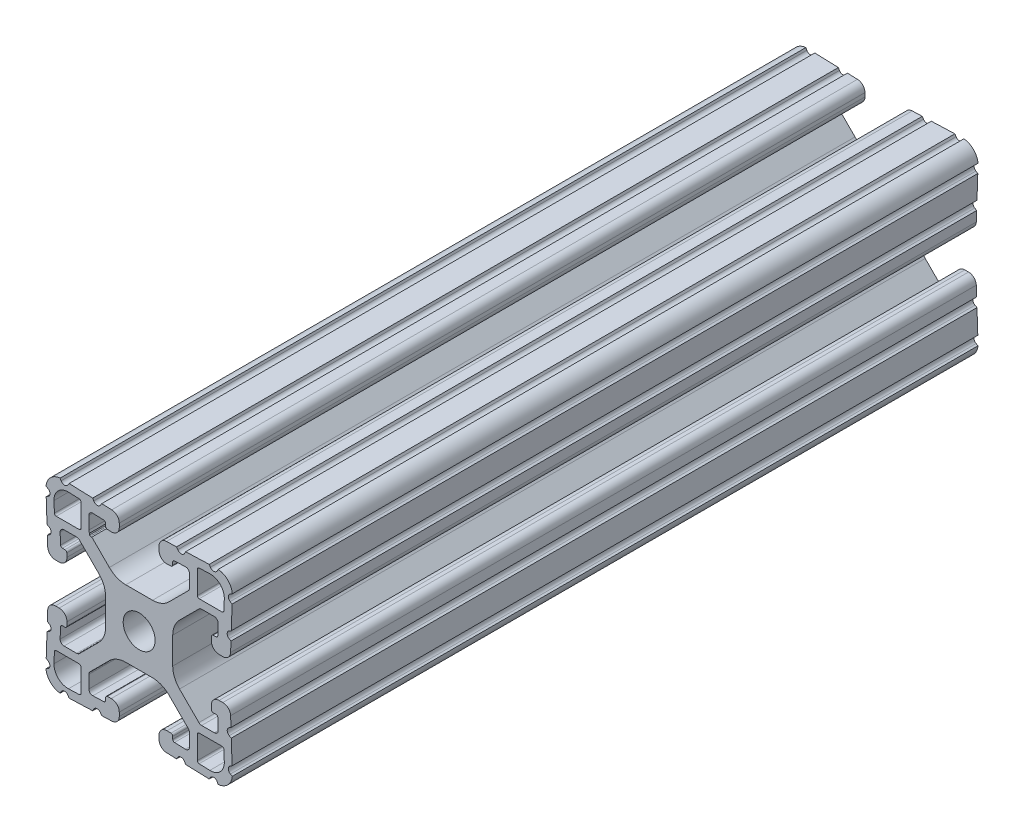
SolidWorks part; units mm, degrees
ref_plane "Front Plane" through (0, 0, 0) normal (0, 0, 1) x (1, 0, 0)
ref_plane "Top Plane" through (0, 0, 0) normal (0, 1, 0) x (1, 0, 0)
ref_plane "Right Plane" through (0, 0, 0) normal (1, 0, 0) x (0, 0, -1)
sketch "Sketch2" plane through (0, 0, 0) normal (0, 0, 1) x (1, 0, 0)
  line L0 (0, 19.05) -> (0, -19.05) construction
  line L1 (-19.05, 0) -> (19.05, 0) construction
  line L2 (4.064, -19.05) -> (19.05, -19.05) construction
  line L3 (19.05, -19.05) -> (19.05, -4.064) construction
  line L4 (4.064, -19.05) -> (4.064, -15.8768) construction
  line L5 (4.064, -15.8768) -> (13.7215, -15.8768) construction
  line L6 (13.7215, -15.8768) -> (4.7027, -6.858) construction
  line L7 (0, 0) -> (19.05, -19.05) construction
  line L8 (19.05, -4.064) -> (15.8768, -4.064) construction
  line L9 (15.8768, -4.064) -> (15.8768, -13.7215) construction
  line L10 (15.8768, -13.7215) -> (6.858, -4.7027) construction
  line L11 (11.3674, -9.2121) -> (9.2121, -11.3674) construction
  line L12 (10.287, -12.4423) -> (10.287, -15.8768) construction
  line L13 (15.7642, -19.0481) -> (4.064, -18.6395) construction
  line L14 (4.064, -18.6395) -> (4.2014, -14.7049) construction
  line L15 (4.2014, -14.7049) -> (6.858, -14.7977) construction
  line L16 (6.858, -14.7977) -> (6.858, -15.8768) construction
  line L17 (19.05, 4.064) -> (19.05, -4.064) construction
  line L18 (-19.05, -19.05) -> (19.05, -19.05) construction
  line L19 (-19.05, -19.05) -> (-19.05, 19.05) construction
  line L20 (-19.05, 19.05) -> (19.05, 19.05) construction
  line L21 (19.05, -19.05) -> (19.05, 19.05) construction
  line L22 (8.5725, -18.7969) -> (8.6004, -17.9973) construction
  line L23 (15.24, -19.0298) -> (15.2679, -18.2301) construction
  circle A0 centre (0, 0) radius 3.2639 construction
  arc A1 (18.1201, -18.1201) -> (15.7642, -19.0481) centre (15.875, -15.875) cw construction
  point P8 (0, -6.858)
  point P16 (10.2898, -10.2898)
  point P28 (11.8872, -11.8872)
  point P34 (8.5725, -18.7969)
  point P36 (15.24, -19.0298)
  point P38 (19.05, 0)
  dimension "D7" = 1.6002
  dimension "Center Hole Diameter" = 6.5278
  dimension "Corner Radius" = 3.175
  dimension "Rail Height" = 19.05
  dimension "Rail Width" = 19.05
  dimension "T-Slot Width" = 4.064
  dimension "Slot Depth" = 12.192
  dimension "D1" = 3.048
  dimension "D3" = 2
  dimension "Flange Thickness" = 3.937
  dimension "D4" = 3.1732
  dimension "D2" = 20.574
  dimension "D5" = 13.716
  dimension "D6" = 7.1628
  dimension "D8" = 15.24
  dimension "D9" = 8.5725
  dimension "D10" = 0.8001
sketch "Sketch3" plane through (0, 0, 0) normal (1, 0, 0) x (0, 0, -1)
  line L0 (-76.2, 19.05) -> (76.2, 19.05) construction
  line L1 (-25.4, 0) -> (25.4, 0) construction
  dimension "Length" = 152.4
  dimension "D1" = 50.8
sketch "Sketch4" plane through (0, 0, 0) normal (0, 0, 1) x (1, 0, 0)
  line L1 (6.858, -14.7977) -> (6.858, -15.8768) construction
  line L2 (11.8872, -12.2682) -> (11.8872, -16.9436)
  line L3 (12.2549, -17.3243) -> (14.4454, -17.4008)
  line L7 (12.2682, -11.8872) -> (16.9436, -11.8872)
  line L9 (17.3243, -12.2549) -> (17.4008, -14.4454)
  line L22 (0, 0) -> (19.05, -19.05) construction
  line L23 (15.7642, -19.0481) -> (5.5961, -18.693)
  line L24 (4.064, -17.1065) -> (4.064, -16.344)
  line L25 (5.7069, -14.7575) -> (6.4903, -14.7848)
  line L26 (6.858, -15.1656) -> (6.858, -15.6891)
  line L27 (7.2257, -16.0699) -> (9.4655, -16.1481)
  line L28 (10.287, -15.3549) -> (10.287, -12.771)
  line L29 (10.0545, -12.2098) -> (6.0939, -8.2492)
  line L30 (2.7353, -6.858) -> (0, -6.858)
  line L31 (13.7215, -15.8768) -> (4.7027, -6.858) construction
  line L32 (4.064, -19.05) -> (19.05, -19.05) construction
  line L33 (4.064, -19.05) -> (4.064, -15.8768) construction
  line L34 (0, 19.05) -> (0, -19.05) construction
  line L35 (0, -3.2639) -> (0, -6.858)
  line L36 (0, 0) -> (19.05, -19.05) construction
  line L46 (10.287, -12.4423) -> (10.287, -15.8768) construction
  line L47 (6.858, -2.7353) -> (6.858, 0)
  line L48 (12.2098, -10.0545) -> (8.2492, -6.0939)
  line L49 (15.3549, -10.287) -> (12.771, -10.287)
  line L50 (16.0699, -7.2257) -> (16.1481, -9.4655)
  line L51 (15.1656, -6.858) -> (15.6891, -6.858)
  line L52 (14.7575, -5.7069) -> (14.7848, -6.4903)
  line L53 (17.1065, -4.064) -> (16.344, -4.064)
  line L54 (19.0481, -15.7642) -> (18.693, -5.5961)
  line L55 (3.2639, 0) -> (6.858, 0)
  arc A1 (14.4454, -17.4008) -> (17.4008, -14.4454) centre (14.5451, -14.5451) ccw
  arc A10 (16.9436, -11.8872) -> (17.3243, -12.2549) centre (16.9436, -12.2682) cw
  arc A12 (19.0481, -15.7642) -> (15.7642, -19.0481) centre (15.875, -15.875) cw
  arc A13 (3.2639, 0) -> (0, -3.2639) centre (0, 0) cw
  circle A14 centre (0, 0) radius 3.2639 construction
  arc A16 (6.0939, -8.2492) -> (2.7353, -6.858) centre (2.7353, -11.6078) ccw
  arc A17 (5.5961, -18.693) -> (4.064, -17.1065) centre (5.6515, -17.1065) cw
  arc A18 (4.064, -16.344) -> (5.7069, -14.7575) centre (5.6515, -16.344) cw
  arc A19 (9.4655, -16.1481) -> (10.287, -15.3549) centre (9.4933, -15.3549) ccw
  arc A20 (10.287, -12.771) -> (10.0545, -12.2098) centre (9.4933, -12.771) ccw
  arc A21 (6.4903, -14.7848) -> (6.858, -15.1656) centre (6.477, -15.1656) cw
  arc A22 (6.858, -15.6891) -> (7.2257, -16.0699) centre (7.239, -15.6891) ccw
  arc A23 (15.6891, -6.858) -> (16.0699, -7.2257) centre (15.6891, -7.239) cw
  arc A24 (14.7848, -6.4903) -> (15.1656, -6.858) centre (15.1656, -6.477) ccw
  arc A25 (12.771, -10.287) -> (12.2098, -10.0545) centre (12.771, -9.4933) cw
  arc A26 (16.1481, -9.4655) -> (15.3549, -10.287) centre (15.3549, -9.4933) cw
  arc A27 (16.344, -4.064) -> (14.7575, -5.7069) centre (16.344, -5.6515) ccw
  arc A28 (18.693, -5.5961) -> (17.1065, -4.064) centre (17.1065, -5.6515) ccw
  arc A29 (8.2492, -6.0939) -> (6.858, -2.7353) centre (11.6078, -2.7353) cw
  arc A30 (15.7642, -19.0481) -> (18.1201, -18.1201) centre (15.875, -15.875) ccw construction
  arc A31 (11.8872, -12.2682) -> (12.2682, -11.8872) centre (12.2682, -12.2682) cw
  arc A32 (11.8872, -16.9436) -> (12.2549, -17.3243) centre (12.2682, -16.9436) ccw
  point P33 (4.064, -18.6395)
  point P42 (6.858, -4.7027)
  point P45 (4.7027, -6.858)
  point P76 (18.6395, -4.064)
  point P89 (11.8872, -11.8872)
  dimension "D2" = 4.7498
  dimension "D3" = 0.7937
  dimension "D5" = 0.381
  dimension "D6" = 1.5875
  dimension "D8" = 2.8575
  dimension "D1" = 2
  dimension "D4" = 2.6784
  dimension "D7" = 1.6002
extrude "Boss-Extrude1" add sketch "Sketch4" along normal mid plane 152.4
sketch "Sketch8" plane through (0, 0, 0) normal (0, 0, 1) x (1, 0, 0)
  line L0 (7.6492, -18.7647) -> (9.4958, -18.8292)
  line L1 (15.7642, -19.0481) -> (4.064, -18.6395) construction
  line L2 (9.4958, -18.8292) -> (9.2789, -18.4213)
  line L3 (7.894, -18.3729) -> (7.6492, -18.7647)
  line L4 (8.5725, -18.7969) -> (8.6004, -17.9973) construction
  line L5 (14.3167, -18.9975) -> (16.1633, -19.062)
  line L7 (16.1633, -19.062) -> (15.9464, -18.6541)
  line L8 (14.5615, -18.6058) -> (14.3167, -18.9975)
  line L9 (15.24, -19.0298) -> (15.2679, -18.2301) construction
  line L10 (0, 0) -> (19.05, -19.05) construction
  line L11 (18.6058, -14.5615) -> (18.9975, -14.3167)
  line L12 (19.062, -16.1633) -> (18.6541, -15.9464)
  line L13 (18.9975, -14.3167) -> (19.062, -16.1633)
  line L14 (18.3729, -7.894) -> (18.7647, -7.6492)
  line L15 (18.8292, -9.4958) -> (18.4213, -9.2789)
  line L16 (18.7647, -7.6492) -> (18.8292, -9.4958)
  arc A0 (9.2789, -18.4213) -> (7.894, -18.3729) centre (8.5725, -18.7969) ccw
  arc A1 (15.9464, -18.6541) -> (14.5615, -18.6058) centre (15.24, -19.0298) ccw
  arc A2 (18.6541, -15.9464) -> (18.6058, -14.5615) centre (19.0298, -15.24) cw
  arc A3 (18.4213, -9.2789) -> (18.3729, -7.894) centre (18.7969, -8.5725) cw
  dimension "D1" = 60
extrude "Cut-Extrude2" cut sketch "Sketch8" against normal through all both and the other way through all
mirror "Mirror1" about plane through (0, 0, 0) normal (1, 0, 0) of bodies 142 134
mirror "Mirror2" about plane through (0, 0, 0) normal (0, 1, 0) of bodies 135
sketch "Sketch5" plane through (0, 0, 0) normal (0, 0, 1) x (1, 0, 0)
  line L0 (-6.0939, 8.2492) -> (-10.0545, 12.2098) construction
  line L1 (-10.1338, 12.508) -> (-10.1338, 12)
  line L2 (-9.9645, 11.8306) -> (-9.6506, 11.8306)
  line L3 (-9.6506, 11.8306) -> (-9.6506, 12.508)
  line L4 (-9.6506, 12.508) -> (-10.1338, 12.508)
  line L5 (-9.9046, 12.0598) -> (-9.9645, 12) construction
  circle A0 centre (-9.9046, 12.0598) radius 0.254 construction
  arc A1 (-10.287, 12.771) -> (-10.0545, 12.2098) centre (-9.4933, 12.771) ccw construction
  arc A2 (-10.1338, 12) -> (-9.9645, 11.8306) centre (-9.9645, 12) ccw
  dimension "D2" = 0.508
  dimension "D3" = 0.1693
  dimension "D1" = 0.7112
  dimension "D4" = 0.508
extrude "Cut-Extrude1" cut sketch "Sketch5" against normal through all both and the other way through all
sketch "Sketch9" plane through (0, 0, 76.2) normal (0, 0, 1) x (1, 0, 0)
  line L4 (-17.3243, -12.2549) -> (-17.4008, -14.4454)
  line L5 (-12.2682, -11.8872) -> (-16.9436, -11.8872)
  line L6 (-11.8872, -16.9436) -> (-11.8872, -12.2682)
  line L7 (-14.4454, -17.4008) -> (-12.2549, -17.3243)
  line L8 (-17.3243, -12.2549) -> (-17.4008, -14.4454)
  line L9 (-12.2682, -11.8872) -> (-16.9436, -11.8872)
  line L10 (-11.8872, -16.9436) -> (-11.8872, -12.2682)
  line L11 (-14.4454, -17.4008) -> (-12.2549, -17.3243)
  line L12 (12.2549, -17.3243) -> (14.4454, -17.4008)
  line L13 (11.8872, -12.2682) -> (11.8872, -16.9436)
  line L14 (16.9436, -11.8872) -> (12.2682, -11.8872)
  line L15 (17.4008, -14.4454) -> (17.3243, -12.2549)
  line L16 (12.2549, -17.3243) -> (14.4454, -17.4008)
  line L17 (11.8872, -12.2682) -> (11.8872, -16.9436)
  line L18 (16.9436, -11.8872) -> (12.2682, -11.8872)
  line L19 (17.4008, -14.4454) -> (17.3243, -12.2549)
  line L20 (17.3243, 12.2549) -> (17.4008, 14.4454)
  line L21 (12.2682, 11.8872) -> (16.9436, 11.8872)
  line L22 (11.8872, 16.9436) -> (11.8872, 12.2682)
  line L23 (14.4454, 17.4008) -> (12.2549, 17.3243)
  line L24 (17.3243, 12.2549) -> (17.4008, 14.4454)
  line L25 (12.2682, 11.8872) -> (16.9436, 11.8872)
  line L26 (11.8872, 16.9436) -> (11.8872, 12.2682)
  line L27 (14.4454, 17.4008) -> (12.2549, 17.3243)
  line L28 (-12.2549, 17.3243) -> (-14.4454, 17.4008)
  line L29 (-11.8872, 12.2682) -> (-11.8872, 16.9436)
  line L30 (-16.9436, 11.8872) -> (-12.2682, 11.8872)
  line L31 (-17.4008, 14.4454) -> (-17.3243, 12.2549)
  line L32 (-12.2549, 17.3243) -> (-14.4454, 17.4008)
  line L33 (-11.8872, 12.2682) -> (-11.8872, 16.9436)
  line L34 (-16.9436, 11.8872) -> (-12.2682, 11.8872)
  line L35 (-17.4008, 14.4454) -> (-17.3243, 12.2549)
  line L102 (-6.0939, 8.2492) -> (-9.6754, 11.8306)
  line L103 (-9.6754, 11.8306) -> (-9.9645, 11.8306)
  line L104 (-10.1338, 12) -> (-10.1338, 12.3023)
  line L105 (-10.287, 12.771) -> (-10.287, 15.3549)
  line L106 (-9.4655, 16.1481) -> (-7.2257, 16.0699)
  line L107 (-6.858, 15.6891) -> (-6.858, 15.1656)
  line L108 (-6.4903, 14.7848) -> (-5.7069, 14.7575)
  line L109 (-4.064, 16.344) -> (-4.064, 17.1065)
  line L110 (-5.5961, 18.693) -> (-7.6492, 18.7647)
  line L111 (-7.6492, 18.7647) -> (-7.894, 18.3729)
  line L112 (-9.2789, 18.4213) -> (-9.4958, 18.8292)
  line L113 (-9.4958, 18.8292) -> (-14.3167, 18.9975)
  line L114 (-14.3167, 18.9975) -> (-14.5615, 18.6058)
  line L115 (-15.9464, 18.6541) -> (-16.1506, 19.038)
  line L116 (-19.038, 16.1506) -> (-18.6541, 15.9464)
  line L117 (-18.6058, 14.5615) -> (-18.9975, 14.3167)
  line L118 (-18.9975, 14.3167) -> (-18.8292, 9.4958)
  line L119 (-18.8292, 9.4958) -> (-18.4213, 9.2789)
  line L120 (-18.3729, 7.894) -> (-18.7647, 7.6492)
  line L121 (-18.7647, 7.6492) -> (-18.693, 5.5961)
  line L122 (-17.1065, 4.064) -> (-16.344, 4.064)
  line L123 (-14.7575, 5.7069) -> (-14.7848, 6.4903)
  line L124 (-15.1656, 6.858) -> (-15.6891, 6.858)
  line L125 (-16.0699, 7.2257) -> (-16.1481, 9.4655)
  line L126 (-15.3549, 10.287) -> (-12.771, 10.287)
  line L127 (-12.2098, 10.0545) -> (-8.2492, 6.0939)
  line L128 (-6.858, 2.7353) -> (-6.858, -2.7353)
  line L129 (-8.2492, -6.0939) -> (-12.2098, -10.0545)
  line L130 (-12.771, -10.287) -> (-15.3549, -10.287)
  line L131 (-16.1481, -9.4655) -> (-16.0699, -7.2257)
  line L132 (-15.6891, -6.858) -> (-15.1656, -6.858)
  line L133 (-14.7848, -6.4903) -> (-14.7575, -5.7069)
  line L134 (-16.344, -4.064) -> (-17.1065, -4.064)
  line L135 (-18.693, -5.5961) -> (-18.7647, -7.6492)
  line L136 (-18.7647, -7.6492) -> (-18.3729, -7.894)
  line L137 (-18.4213, -9.2789) -> (-18.8292, -9.4958)
  line L138 (-18.8292, -9.4958) -> (-18.9975, -14.3167)
  line L139 (-18.9975, -14.3167) -> (-18.6058, -14.5615)
  line L140 (-18.6541, -15.9464) -> (-19.038, -16.1506)
  line L141 (-16.1506, -19.038) -> (-15.9464, -18.6541)
  line L142 (-14.5615, -18.6058) -> (-14.3167, -18.9975)
  line L143 (-14.3167, -18.9975) -> (-9.4958, -18.8292)
  line L144 (-9.4958, -18.8292) -> (-9.2789, -18.4213)
  line L145 (-7.894, -18.3729) -> (-7.6492, -18.7647)
  line L146 (-7.6492, -18.7647) -> (-5.5961, -18.693)
  line L147 (-4.064, -17.1065) -> (-4.064, -16.344)
  line L148 (-5.7069, -14.7575) -> (-6.4903, -14.7848)
  line L149 (-6.858, -15.1656) -> (-6.858, -15.6891)
  line L150 (-7.2257, -16.0699) -> (-9.4655, -16.1481)
  line L151 (-10.287, -15.3549) -> (-10.287, -12.771)
  line L152 (-10.0545, -12.2098) -> (-6.0939, -8.2492)
  line L153 (-2.7353, -6.858) -> (2.7353, -6.858)
  line L154 (6.0939, -8.2492) -> (10.0545, -12.2098)
  line L155 (10.287, -12.771) -> (10.287, -15.3549)
  line L156 (9.4655, -16.1481) -> (7.2257, -16.0699)
  line L157 (6.858, -15.6891) -> (6.858, -15.1656)
  line L158 (6.4903, -14.7848) -> (5.7069, -14.7575)
  line L159 (4.064, -16.344) -> (4.064, -17.1065)
  line L160 (5.5961, -18.693) -> (7.6492, -18.7647)
  line L161 (7.6492, -18.7647) -> (7.894, -18.3729)
  line L162 (9.2789, -18.4213) -> (9.4958, -18.8292)
  line L163 (9.4958, -18.8292) -> (14.3167, -18.9975)
  line L164 (14.3167, -18.9975) -> (14.5615, -18.6058)
  line L165 (15.9464, -18.6541) -> (16.1506, -19.038)
  line L166 (19.038, -16.1506) -> (18.6541, -15.9464)
  line L167 (18.6058, -14.5615) -> (18.9975, -14.3167)
  line L168 (18.9975, -14.3167) -> (18.8292, -9.4958)
  line L169 (18.8292, -9.4958) -> (18.4213, -9.2789)
  line L170 (18.3729, -7.894) -> (18.7647, -7.6492)
  line L171 (18.7647, -7.6492) -> (18.693, -5.5961)
  line L172 (17.1065, -4.064) -> (16.344, -4.064)
  line L173 (14.7575, -5.7069) -> (14.7848, -6.4903)
  line L174 (15.1656, -6.858) -> (15.6891, -6.858)
  line L175 (16.0699, -7.2257) -> (16.1481, -9.4655)
  line L176 (15.3549, -10.287) -> (12.771, -10.287)
  line L177 (12.2098, -10.0545) -> (8.2492, -6.0939)
  line L178 (6.858, -2.7353) -> (6.858, 2.7353)
  line L179 (8.2492, 6.0939) -> (12.2098, 10.0545)
  line L180 (12.771, 10.287) -> (15.3549, 10.287)
  line L181 (16.1481, 9.4655) -> (16.0699, 7.2257)
  line L182 (15.6891, 6.858) -> (15.1656, 6.858)
  line L183 (14.7848, 6.4903) -> (14.7575, 5.7069)
  line L184 (16.344, 4.064) -> (17.1065, 4.064)
  line L185 (18.693, 5.5961) -> (18.7647, 7.6492)
  line L186 (18.7647, 7.6492) -> (18.3729, 7.894)
  line L187 (18.4213, 9.2789) -> (18.8292, 9.4958)
  line L188 (18.8292, 9.4958) -> (18.9975, 14.3167)
  line L189 (18.9975, 14.3167) -> (18.6058, 14.5615)
  line L190 (18.6541, 15.9464) -> (19.038, 16.1506)
  line L191 (16.1506, 19.038) -> (15.9464, 18.6541)
  line L192 (14.5615, 18.6058) -> (14.3167, 18.9975)
  line L193 (14.3167, 18.9975) -> (9.4958, 18.8292)
  line L194 (9.4958, 18.8292) -> (9.2789, 18.4213)
  line L195 (7.894, 18.3729) -> (7.6492, 18.7647)
  line L196 (7.6492, 18.7647) -> (5.5961, 18.693)
  line L197 (4.064, 17.1065) -> (4.064, 16.344)
  line L198 (5.7069, 14.7575) -> (6.4903, 14.7848)
  line L199 (6.858, 15.1656) -> (6.858, 15.6891)
  line L200 (7.2257, 16.0699) -> (9.4655, 16.1481)
  line L201 (10.287, 15.3549) -> (10.287, 12.771)
  line L202 (10.0545, 12.2098) -> (6.0939, 8.2492)
  line L203 (2.7353, 6.858) -> (-2.7353, 6.858)
  line L204 (-6.0939, 8.2492) -> (-9.6754, 11.8306)
  line L205 (-9.6754, 11.8306) -> (-9.9645, 11.8306)
  line L206 (-10.1338, 12) -> (-10.1338, 12.3023)
  line L207 (-10.287, 12.771) -> (-10.287, 15.3549)
  line L208 (-9.4655, 16.1481) -> (-7.2257, 16.0699)
  line L209 (-6.858, 15.6891) -> (-6.858, 15.1656)
  line L210 (-6.4903, 14.7848) -> (-5.7069, 14.7575)
  line L211 (-4.064, 16.344) -> (-4.064, 17.1065)
  line L212 (-5.5961, 18.693) -> (-7.6492, 18.7647)
  line L213 (-7.6492, 18.7647) -> (-7.894, 18.3729)
  line L214 (-9.2789, 18.4213) -> (-9.4958, 18.8292)
  line L215 (-9.4958, 18.8292) -> (-14.3167, 18.9975)
  line L216 (-14.3167, 18.9975) -> (-14.5615, 18.6058)
  line L217 (-15.9464, 18.6541) -> (-16.1506, 19.038)
  line L218 (-19.038, 16.1506) -> (-18.6541, 15.9464)
  line L219 (-18.6058, 14.5615) -> (-18.9975, 14.3167)
  line L220 (-18.9975, 14.3167) -> (-18.8292, 9.4958)
  line L221 (-18.8292, 9.4958) -> (-18.4213, 9.2789)
  line L222 (-18.3729, 7.894) -> (-18.7647, 7.6492)
  line L223 (-18.7647, 7.6492) -> (-18.693, 5.5961)
  line L224 (-17.1065, 4.064) -> (-16.344, 4.064)
  line L225 (-14.7575, 5.7069) -> (-14.7848, 6.4903)
  line L226 (-15.1656, 6.858) -> (-15.6891, 6.858)
  line L227 (-16.0699, 7.2257) -> (-16.1481, 9.4655)
  line L228 (-15.3549, 10.287) -> (-12.771, 10.287)
  line L229 (-12.2098, 10.0545) -> (-8.2492, 6.0939)
  line L230 (-6.858, 2.7353) -> (-6.858, -2.7353)
  line L231 (-8.2492, -6.0939) -> (-12.2098, -10.0545)
  line L232 (-12.771, -10.287) -> (-15.3549, -10.287)
  line L233 (-16.1481, -9.4655) -> (-16.0699, -7.2257)
  line L234 (-15.6891, -6.858) -> (-15.1656, -6.858)
  line L235 (-14.7848, -6.4903) -> (-14.7575, -5.7069)
  line L236 (-16.344, -4.064) -> (-17.1065, -4.064)
  line L237 (-18.693, -5.5961) -> (-18.7647, -7.6492)
  line L238 (-18.7647, -7.6492) -> (-18.3729, -7.894)
  line L239 (-18.4213, -9.2789) -> (-18.8292, -9.4958)
  line L240 (-18.8292, -9.4958) -> (-18.9975, -14.3167)
  line L241 (-18.9975, -14.3167) -> (-18.6058, -14.5615)
  line L242 (-18.6541, -15.9464) -> (-19.038, -16.1506)
  line L243 (-16.1506, -19.038) -> (-15.9464, -18.6541)
  line L244 (-14.5615, -18.6058) -> (-14.3167, -18.9975)
  line L245 (-14.3167, -18.9975) -> (-9.4958, -18.8292)
  line L246 (-9.4958, -18.8292) -> (-9.2789, -18.4213)
  line L247 (-7.894, -18.3729) -> (-7.6492, -18.7647)
  line L248 (-7.6492, -18.7647) -> (-5.5961, -18.693)
  line L249 (-4.064, -17.1065) -> (-4.064, -16.344)
  line L250 (-5.7069, -14.7575) -> (-6.4903, -14.7848)
  line L251 (-6.858, -15.1656) -> (-6.858, -15.6891)
  line L252 (-7.2257, -16.0699) -> (-9.4655, -16.1481)
  line L253 (-10.287, -15.3549) -> (-10.287, -12.771)
  line L254 (-10.0545, -12.2098) -> (-6.0939, -8.2492)
  line L255 (-2.7353, -6.858) -> (2.7353, -6.858)
  line L256 (6.0939, -8.2492) -> (10.0545, -12.2098)
  line L257 (10.287, -12.771) -> (10.287, -15.3549)
  line L258 (9.4655, -16.1481) -> (7.2257, -16.0699)
  line L259 (6.858, -15.6891) -> (6.858, -15.1656)
  line L260 (6.4903, -14.7848) -> (5.7069, -14.7575)
  line L261 (4.064, -16.344) -> (4.064, -17.1065)
  line L262 (5.5961, -18.693) -> (7.6492, -18.7647)
  line L263 (7.6492, -18.7647) -> (7.894, -18.3729)
  line L264 (9.2789, -18.4213) -> (9.4958, -18.8292)
  line L265 (9.4958, -18.8292) -> (14.3167, -18.9975)
  line L266 (14.3167, -18.9975) -> (14.5615, -18.6058)
  line L267 (15.9464, -18.6541) -> (16.1506, -19.038)
  line L268 (19.038, -16.1506) -> (18.6541, -15.9464)
  line L269 (18.6058, -14.5615) -> (18.9975, -14.3167)
  line L270 (18.9975, -14.3167) -> (18.8292, -9.4958)
  line L271 (18.8292, -9.4958) -> (18.4213, -9.2789)
  line L272 (18.3729, -7.894) -> (18.7647, -7.6492)
  line L273 (18.7647, -7.6492) -> (18.693, -5.5961)
  line L274 (17.1065, -4.064) -> (16.344, -4.064)
  line L275 (14.7575, -5.7069) -> (14.7848, -6.4903)
  line L276 (15.1656, -6.858) -> (15.6891, -6.858)
  line L277 (16.0699, -7.2257) -> (16.1481, -9.4655)
  line L278 (15.3549, -10.287) -> (12.771, -10.287)
  line L279 (12.2098, -10.0545) -> (8.2492, -6.0939)
  line L280 (6.858, -2.7353) -> (6.858, 2.7353)
  line L281 (8.2492, 6.0939) -> (12.2098, 10.0545)
  line L282 (12.771, 10.287) -> (15.3549, 10.287)
  line L283 (16.1481, 9.4655) -> (16.0699, 7.2257)
  line L284 (15.6891, 6.858) -> (15.1656, 6.858)
  line L285 (14.7848, 6.4903) -> (14.7575, 5.7069)
  line L286 (16.344, 4.064) -> (17.1065, 4.064)
  line L287 (18.693, 5.5961) -> (18.7647, 7.6492)
  line L288 (18.7647, 7.6492) -> (18.3729, 7.894)
  line L289 (18.4213, 9.2789) -> (18.8292, 9.4958)
  line L290 (18.8292, 9.4958) -> (18.9975, 14.3167)
  line L291 (18.9975, 14.3167) -> (18.6058, 14.5615)
  line L292 (18.6541, 15.9464) -> (19.038, 16.1506)
  line L293 (16.1506, 19.038) -> (15.9464, 18.6541)
  line L294 (14.5615, 18.6058) -> (14.3167, 18.9975)
  line L295 (14.3167, 18.9975) -> (9.4958, 18.8292)
  line L296 (9.4958, 18.8292) -> (9.2789, 18.4213)
  line L297 (7.894, 18.3729) -> (7.6492, 18.7647)
  line L298 (7.6492, 18.7647) -> (5.5961, 18.693)
  line L299 (4.064, 17.1065) -> (4.064, 16.344)
  line L300 (5.7069, 14.7575) -> (6.4903, 14.7848)
  line L301 (6.858, 15.1656) -> (6.858, 15.6891)
  line L302 (7.2257, 16.0699) -> (9.4655, 16.1481)
  line L303 (10.287, 15.3549) -> (10.287, 12.771)
  line L304 (10.0545, 12.2098) -> (6.0939, 8.2492)
  line L305 (2.7353, 6.858) -> (-2.7353, 6.858)
  circle A1 centre (0, 0) radius 3.2639
  circle A2 centre (0, 0) radius 3.2639
  arc A6 (-17.4008, -14.4454) -> (-14.4454, -17.4008) centre (-14.5451, -14.5451) ccw
  arc A7 (-16.9436, -11.8872) -> (-17.3243, -12.2549) centre (-16.9436, -12.2682) ccw
  arc A8 (-11.8872, -12.2682) -> (-12.2682, -11.8872) centre (-12.2682, -12.2682) ccw
  arc A9 (-12.2549, -17.3243) -> (-11.8872, -16.9436) centre (-12.2682, -16.9436) ccw
  arc A10 (-17.4008, -14.4454) -> (-14.4454, -17.4008) centre (-14.5451, -14.5451) ccw
  arc A11 (-16.9436, -11.8872) -> (-17.3243, -12.2549) centre (-16.9436, -12.2682) ccw
  arc A12 (-11.8872, -12.2682) -> (-12.2682, -11.8872) centre (-12.2682, -12.2682) ccw
  arc A13 (-12.2549, -17.3243) -> (-11.8872, -16.9436) centre (-12.2682, -16.9436) ccw
  arc A14 (14.4454, -17.4008) -> (17.4008, -14.4454) centre (14.5451, -14.5451) ccw
  arc A15 (11.8872, -16.9436) -> (12.2549, -17.3243) centre (12.2682, -16.9436) ccw
  arc A16 (12.2682, -11.8872) -> (11.8872, -12.2682) centre (12.2682, -12.2682) ccw
  arc A17 (17.3243, -12.2549) -> (16.9436, -11.8872) centre (16.9436, -12.2682) ccw
  arc A18 (14.4454, -17.4008) -> (17.4008, -14.4454) centre (14.5451, -14.5451) ccw
  arc A19 (11.8872, -16.9436) -> (12.2549, -17.3243) centre (12.2682, -16.9436) ccw
  arc A20 (12.2682, -11.8872) -> (11.8872, -12.2682) centre (12.2682, -12.2682) ccw
  arc A21 (17.3243, -12.2549) -> (16.9436, -11.8872) centre (16.9436, -12.2682) ccw
  arc A22 (17.4008, 14.4454) -> (14.4454, 17.4008) centre (14.5451, 14.5451) ccw
  arc A23 (16.9436, 11.8872) -> (17.3243, 12.2549) centre (16.9436, 12.2682) ccw
  arc A24 (11.8872, 12.2682) -> (12.2682, 11.8872) centre (12.2682, 12.2682) ccw
  arc A25 (12.2549, 17.3243) -> (11.8872, 16.9436) centre (12.2682, 16.9436) ccw
  arc A26 (17.4008, 14.4454) -> (14.4454, 17.4008) centre (14.5451, 14.5451) ccw
  arc A27 (16.9436, 11.8872) -> (17.3243, 12.2549) centre (16.9436, 12.2682) ccw
  arc A28 (11.8872, 12.2682) -> (12.2682, 11.8872) centre (12.2682, 12.2682) ccw
  arc A29 (12.2549, 17.3243) -> (11.8872, 16.9436) centre (12.2682, 16.9436) ccw
  arc A30 (-14.4454, 17.4008) -> (-17.4008, 14.4454) centre (-14.5451, 14.5451) ccw
  arc A31 (-11.8872, 16.9436) -> (-12.2549, 17.3243) centre (-12.2682, 16.9436) ccw
  arc A32 (-12.2682, 11.8872) -> (-11.8872, 12.2682) centre (-12.2682, 12.2682) ccw
  arc A33 (-17.3243, 12.2549) -> (-16.9436, 11.8872) centre (-16.9436, 12.2682) ccw
  arc A34 (-14.4454, 17.4008) -> (-17.4008, 14.4454) centre (-14.5451, 14.5451) ccw
  arc A35 (-11.8872, 16.9436) -> (-12.2549, 17.3243) centre (-12.2682, 16.9436) ccw
  arc A36 (-12.2682, 11.8872) -> (-11.8872, 12.2682) centre (-12.2682, 12.2682) ccw
  arc A37 (-17.3243, 12.2549) -> (-16.9436, 11.8872) centre (-16.9436, 12.2682) ccw
  arc A77 (-10.1338, 12) -> (-9.9645, 11.8306) centre (-9.9645, 12) ccw
  arc A78 (-10.287, 12.771) -> (-10.1338, 12.3023) centre (-9.4933, 12.771) ccw
  arc A79 (-9.4655, 16.1481) -> (-10.287, 15.3549) centre (-9.4933, 15.3549) ccw
  arc A80 (-6.858, 15.6891) -> (-7.2257, 16.0699) centre (-7.239, 15.6891) ccw
  arc A81 (-6.858, 15.1656) -> (-6.4903, 14.7848) centre (-6.477, 15.1656) ccw
  arc A82 (-5.7069, 14.7575) -> (-4.064, 16.344) centre (-5.6515, 16.344) ccw
  arc A83 (-4.064, 17.1065) -> (-5.5961, 18.693) centre (-5.6515, 17.1065) ccw
  arc A84 (-9.2789, 18.4213) -> (-7.894, 18.3729) centre (-8.5725, 18.7969) ccw
  arc A85 (-15.9464, 18.6541) -> (-14.5615, 18.6058) centre (-15.24, 19.0298) ccw
  arc A86 (-16.1506, 19.038) -> (-19.038, 16.1506) centre (-15.875, 15.875) ccw
  arc A87 (-18.6058, 14.5615) -> (-18.6541, 15.9464) centre (-19.0298, 15.24) ccw
  arc A88 (-18.3729, 7.894) -> (-18.4213, 9.2789) centre (-18.7969, 8.5725) ccw
  arc A89 (-18.693, 5.5961) -> (-17.1065, 4.064) centre (-17.1065, 5.6515) ccw
  arc A90 (-16.344, 4.064) -> (-14.7575, 5.7069) centre (-16.344, 5.6515) ccw
  arc A91 (-14.7848, 6.4903) -> (-15.1656, 6.858) centre (-15.1656, 6.477) ccw
  arc A92 (-16.0699, 7.2257) -> (-15.6891, 6.858) centre (-15.6891, 7.239) ccw
  arc A93 (-15.3549, 10.287) -> (-16.1481, 9.4655) centre (-15.3549, 9.4933) ccw
  arc A94 (-12.2098, 10.0545) -> (-12.771, 10.287) centre (-12.771, 9.4933) ccw
  arc A95 (-6.858, 2.7353) -> (-8.2492, 6.0939) centre (-11.6078, 2.7353) ccw
  arc A96 (-8.2492, -6.0939) -> (-6.858, -2.7353) centre (-11.6078, -2.7353) ccw
  arc A97 (-12.771, -10.287) -> (-12.2098, -10.0545) centre (-12.771, -9.4933) ccw
  arc A98 (-16.1481, -9.4655) -> (-15.3549, -10.287) centre (-15.3549, -9.4933) ccw
  arc A99 (-15.6891, -6.858) -> (-16.0699, -7.2257) centre (-15.6891, -7.239) ccw
  arc A100 (-15.1656, -6.858) -> (-14.7848, -6.4903) centre (-15.1656, -6.477) ccw
  arc A101 (-14.7575, -5.7069) -> (-16.344, -4.064) centre (-16.344, -5.6515) ccw
  arc A102 (-17.1065, -4.064) -> (-18.693, -5.5961) centre (-17.1065, -5.6515) ccw
  arc A103 (-18.4213, -9.2789) -> (-18.3729, -7.894) centre (-18.7969, -8.5725) ccw
  arc A104 (-18.6541, -15.9464) -> (-18.6058, -14.5615) centre (-19.0298, -15.24) ccw
  arc A105 (-19.038, -16.1506) -> (-16.1506, -19.038) centre (-15.875, -15.875) ccw
  arc A106 (-14.5615, -18.6058) -> (-15.9464, -18.6541) centre (-15.24, -19.0298) ccw
  arc A107 (-7.894, -18.3729) -> (-9.2789, -18.4213) centre (-8.5725, -18.7969) ccw
  arc A108 (-5.5961, -18.693) -> (-4.064, -17.1065) centre (-5.6515, -17.1065) ccw
  arc A109 (-4.064, -16.344) -> (-5.7069, -14.7575) centre (-5.6515, -16.344) ccw
  arc A110 (-6.4903, -14.7848) -> (-6.858, -15.1656) centre (-6.477, -15.1656) ccw
  arc A111 (-7.2257, -16.0699) -> (-6.858, -15.6891) centre (-7.239, -15.6891) ccw
  arc A112 (-10.287, -15.3549) -> (-9.4655, -16.1481) centre (-9.4933, -15.3549) ccw
  arc A113 (-10.0545, -12.2098) -> (-10.287, -12.771) centre (-9.4933, -12.771) ccw
  arc A114 (-2.7353, -6.858) -> (-6.0939, -8.2492) centre (-2.7353, -11.6078) ccw
  arc A115 (6.0939, -8.2492) -> (2.7353, -6.858) centre (2.7353, -11.6078) ccw
  arc A116 (10.287, -12.771) -> (10.0545, -12.2098) centre (9.4933, -12.771) ccw
  arc A117 (9.4655, -16.1481) -> (10.287, -15.3549) centre (9.4933, -15.3549) ccw
  arc A118 (6.858, -15.6891) -> (7.2257, -16.0699) centre (7.239, -15.6891) ccw
  arc A119 (6.858, -15.1656) -> (6.4903, -14.7848) centre (6.477, -15.1656) ccw
  arc A120 (5.7069, -14.7575) -> (4.064, -16.344) centre (5.6515, -16.344) ccw
  arc A121 (4.064, -17.1065) -> (5.5961, -18.693) centre (5.6515, -17.1065) ccw
  arc A122 (9.2789, -18.4213) -> (7.894, -18.3729) centre (8.5725, -18.7969) ccw
  arc A123 (15.9464, -18.6541) -> (14.5615, -18.6058) centre (15.24, -19.0298) ccw
  arc A124 (16.1506, -19.038) -> (19.038, -16.1506) centre (15.875, -15.875) ccw
  arc A125 (18.6058, -14.5615) -> (18.6541, -15.9464) centre (19.0298, -15.24) ccw
  arc A126 (18.3729, -7.894) -> (18.4213, -9.2789) centre (18.7969, -8.5725) ccw
  arc A127 (18.693, -5.5961) -> (17.1065, -4.064) centre (17.1065, -5.6515) ccw
  arc A128 (16.344, -4.064) -> (14.7575, -5.7069) centre (16.344, -5.6515) ccw
  arc A129 (14.7848, -6.4903) -> (15.1656, -6.858) centre (15.1656, -6.477) ccw
  arc A130 (16.0699, -7.2257) -> (15.6891, -6.858) centre (15.6891, -7.239) ccw
  arc A131 (15.3549, -10.287) -> (16.1481, -9.4655) centre (15.3549, -9.4933) ccw
  arc A132 (12.2098, -10.0545) -> (12.771, -10.287) centre (12.771, -9.4933) ccw
  arc A133 (6.858, -2.7353) -> (8.2492, -6.0939) centre (11.6078, -2.7353) ccw
  arc A134 (8.2492, 6.0939) -> (6.858, 2.7353) centre (11.6078, 2.7353) ccw
  arc A135 (12.771, 10.287) -> (12.2098, 10.0545) centre (12.771, 9.4933) ccw
  arc A136 (16.1481, 9.4655) -> (15.3549, 10.287) centre (15.3549, 9.4933) ccw
  arc A137 (15.6891, 6.858) -> (16.0699, 7.2257) centre (15.6891, 7.239) ccw
  arc A138 (15.1656, 6.858) -> (14.7848, 6.4903) centre (15.1656, 6.477) ccw
  arc A139 (14.7575, 5.7069) -> (16.344, 4.064) centre (16.344, 5.6515) ccw
  arc A140 (17.1065, 4.064) -> (18.693, 5.5961) centre (17.1065, 5.6515) ccw
  arc A141 (18.4213, 9.2789) -> (18.3729, 7.894) centre (18.7969, 8.5725) ccw
  arc A142 (18.6541, 15.9464) -> (18.6058, 14.5615) centre (19.0298, 15.24) ccw
  arc A143 (19.038, 16.1506) -> (16.1506, 19.038) centre (15.875, 15.875) ccw
  arc A144 (14.5615, 18.6058) -> (15.9464, 18.6541) centre (15.24, 19.0298) ccw
  arc A145 (7.894, 18.3729) -> (9.2789, 18.4213) centre (8.5725, 18.7969) ccw
  arc A146 (5.5961, 18.693) -> (4.064, 17.1065) centre (5.6515, 17.1065) ccw
  arc A147 (4.064, 16.344) -> (5.7069, 14.7575) centre (5.6515, 16.344) ccw
  arc A148 (6.4903, 14.7848) -> (6.858, 15.1656) centre (6.477, 15.1656) ccw
  arc A149 (7.2257, 16.0699) -> (6.858, 15.6891) centre (7.239, 15.6891) ccw
  arc A150 (10.287, 15.3549) -> (9.4655, 16.1481) centre (9.4933, 15.3549) ccw
  arc A151 (10.0545, 12.2098) -> (10.287, 12.771) centre (9.4933, 12.771) ccw
  arc A152 (2.7353, 6.858) -> (6.0939, 8.2492) centre (2.7353, 11.6078) ccw
  arc A153 (-6.0939, 8.2492) -> (-2.7353, 6.858) centre (-2.7353, 11.6078) ccw
  arc A154 (-10.1338, 12) -> (-9.9645, 11.8306) centre (-9.9645, 12) ccw
  arc A155 (-10.287, 12.771) -> (-10.1338, 12.3023) centre (-9.4933, 12.771) ccw
  arc A156 (-9.4655, 16.1481) -> (-10.287, 15.3549) centre (-9.4933, 15.3549) ccw
  arc A157 (-6.858, 15.6891) -> (-7.2257, 16.0699) centre (-7.239, 15.6891) ccw
  arc A158 (-6.858, 15.1656) -> (-6.4903, 14.7848) centre (-6.477, 15.1656) ccw
  arc A159 (-5.7069, 14.7575) -> (-4.064, 16.344) centre (-5.6515, 16.344) ccw
  arc A160 (-4.064, 17.1065) -> (-5.5961, 18.693) centre (-5.6515, 17.1065) ccw
  arc A161 (-9.2789, 18.4213) -> (-7.894, 18.3729) centre (-8.5725, 18.7969) ccw
  arc A162 (-15.9464, 18.6541) -> (-14.5615, 18.6058) centre (-15.24, 19.0298) ccw
  arc A163 (-16.1506, 19.038) -> (-19.038, 16.1506) centre (-15.875, 15.875) ccw
  arc A164 (-18.6058, 14.5615) -> (-18.6541, 15.9464) centre (-19.0298, 15.24) ccw
  arc A165 (-18.3729, 7.894) -> (-18.4213, 9.2789) centre (-18.7969, 8.5725) ccw
  arc A166 (-18.693, 5.5961) -> (-17.1065, 4.064) centre (-17.1065, 5.6515) ccw
  arc A167 (-16.344, 4.064) -> (-14.7575, 5.7069) centre (-16.344, 5.6515) ccw
  arc A168 (-14.7848, 6.4903) -> (-15.1656, 6.858) centre (-15.1656, 6.477) ccw
  arc A169 (-16.0699, 7.2257) -> (-15.6891, 6.858) centre (-15.6891, 7.239) ccw
  arc A170 (-15.3549, 10.287) -> (-16.1481, 9.4655) centre (-15.3549, 9.4933) ccw
  arc A171 (-12.2098, 10.0545) -> (-12.771, 10.287) centre (-12.771, 9.4933) ccw
  arc A172 (-6.858, 2.7353) -> (-8.2492, 6.0939) centre (-11.6078, 2.7353) ccw
  arc A173 (-8.2492, -6.0939) -> (-6.858, -2.7353) centre (-11.6078, -2.7353) ccw
  arc A174 (-12.771, -10.287) -> (-12.2098, -10.0545) centre (-12.771, -9.4933) ccw
  arc A175 (-16.1481, -9.4655) -> (-15.3549, -10.287) centre (-15.3549, -9.4933) ccw
  arc A176 (-15.6891, -6.858) -> (-16.0699, -7.2257) centre (-15.6891, -7.239) ccw
  arc A177 (-15.1656, -6.858) -> (-14.7848, -6.4903) centre (-15.1656, -6.477) ccw
  arc A178 (-14.7575, -5.7069) -> (-16.344, -4.064) centre (-16.344, -5.6515) ccw
  arc A179 (-17.1065, -4.064) -> (-18.693, -5.5961) centre (-17.1065, -5.6515) ccw
  arc A180 (-18.4213, -9.2789) -> (-18.3729, -7.894) centre (-18.7969, -8.5725) ccw
  arc A181 (-18.6541, -15.9464) -> (-18.6058, -14.5615) centre (-19.0298, -15.24) ccw
  arc A182 (-19.038, -16.1506) -> (-16.1506, -19.038) centre (-15.875, -15.875) ccw
  arc A183 (-14.5615, -18.6058) -> (-15.9464, -18.6541) centre (-15.24, -19.0298) ccw
  arc A184 (-7.894, -18.3729) -> (-9.2789, -18.4213) centre (-8.5725, -18.7969) ccw
  arc A185 (-5.5961, -18.693) -> (-4.064, -17.1065) centre (-5.6515, -17.1065) ccw
  arc A186 (-4.064, -16.344) -> (-5.7069, -14.7575) centre (-5.6515, -16.344) ccw
  arc A187 (-6.4903, -14.7848) -> (-6.858, -15.1656) centre (-6.477, -15.1656) ccw
  arc A188 (-7.2257, -16.0699) -> (-6.858, -15.6891) centre (-7.239, -15.6891) ccw
  arc A189 (-10.287, -15.3549) -> (-9.4655, -16.1481) centre (-9.4933, -15.3549) ccw
  arc A190 (-10.0545, -12.2098) -> (-10.287, -12.771) centre (-9.4933, -12.771) ccw
  arc A191 (-2.7353, -6.858) -> (-6.0939, -8.2492) centre (-2.7353, -11.6078) ccw
  arc A192 (6.0939, -8.2492) -> (2.7353, -6.858) centre (2.7353, -11.6078) ccw
  arc A193 (10.287, -12.771) -> (10.0545, -12.2098) centre (9.4933, -12.771) ccw
  arc A194 (9.4655, -16.1481) -> (10.287, -15.3549) centre (9.4933, -15.3549) ccw
  arc A195 (6.858, -15.6891) -> (7.2257, -16.0699) centre (7.239, -15.6891) ccw
  arc A196 (6.858, -15.1656) -> (6.4903, -14.7848) centre (6.477, -15.1656) ccw
  arc A197 (5.7069, -14.7575) -> (4.064, -16.344) centre (5.6515, -16.344) ccw
  arc A198 (4.064, -17.1065) -> (5.5961, -18.693) centre (5.6515, -17.1065) ccw
  arc A199 (9.2789, -18.4213) -> (7.894, -18.3729) centre (8.5725, -18.7969) ccw
  arc A200 (15.9464, -18.6541) -> (14.5615, -18.6058) centre (15.24, -19.0298) ccw
  arc A201 (16.1506, -19.038) -> (19.038, -16.1506) centre (15.875, -15.875) ccw
  arc A202 (18.6058, -14.5615) -> (18.6541, -15.9464) centre (19.0298, -15.24) ccw
  arc A203 (18.3729, -7.894) -> (18.4213, -9.2789) centre (18.7969, -8.5725) ccw
  arc A204 (18.693, -5.5961) -> (17.1065, -4.064) centre (17.1065, -5.6515) ccw
  arc A205 (16.344, -4.064) -> (14.7575, -5.7069) centre (16.344, -5.6515) ccw
  arc A206 (14.7848, -6.4903) -> (15.1656, -6.858) centre (15.1656, -6.477) ccw
  arc A207 (16.0699, -7.2257) -> (15.6891, -6.858) centre (15.6891, -7.239) ccw
  arc A208 (15.3549, -10.287) -> (16.1481, -9.4655) centre (15.3549, -9.4933) ccw
  arc A209 (12.2098, -10.0545) -> (12.771, -10.287) centre (12.771, -9.4933) ccw
  arc A210 (6.858, -2.7353) -> (8.2492, -6.0939) centre (11.6078, -2.7353) ccw
  arc A211 (8.2492, 6.0939) -> (6.858, 2.7353) centre (11.6078, 2.7353) ccw
  arc A212 (12.771, 10.287) -> (12.2098, 10.0545) centre (12.771, 9.4933) ccw
  arc A213 (16.1481, 9.4655) -> (15.3549, 10.287) centre (15.3549, 9.4933) ccw
  arc A214 (15.6891, 6.858) -> (16.0699, 7.2257) centre (15.6891, 7.239) ccw
  arc A215 (15.1656, 6.858) -> (14.7848, 6.4903) centre (15.1656, 6.477) ccw
  arc A216 (14.7575, 5.7069) -> (16.344, 4.064) centre (16.344, 5.6515) ccw
  arc A217 (17.1065, 4.064) -> (18.693, 5.5961) centre (17.1065, 5.6515) ccw
  arc A218 (18.4213, 9.2789) -> (18.3729, 7.894) centre (18.7969, 8.5725) ccw
  arc A219 (18.6541, 15.9464) -> (18.6058, 14.5615) centre (19.0298, 15.24) ccw
  arc A220 (19.038, 16.1506) -> (16.1506, 19.038) centre (15.875, 15.875) ccw
  arc A221 (14.5615, 18.6058) -> (15.9464, 18.6541) centre (15.24, 19.0298) ccw
  arc A222 (7.894, 18.3729) -> (9.2789, 18.4213) centre (8.5725, 18.7969) ccw
  arc A223 (5.5961, 18.693) -> (4.064, 17.1065) centre (5.6515, 17.1065) ccw
  arc A224 (4.064, 16.344) -> (5.7069, 14.7575) centre (5.6515, 16.344) ccw
  arc A225 (6.4903, 14.7848) -> (6.858, 15.1656) centre (6.477, 15.1656) ccw
  arc A226 (7.2257, 16.0699) -> (6.858, 15.6891) centre (7.239, 15.6891) ccw
  arc A227 (10.287, 15.3549) -> (9.4655, 16.1481) centre (9.4933, 15.3549) ccw
  arc A228 (10.0545, 12.2098) -> (10.287, 12.771) centre (9.4933, 12.771) ccw
  arc A229 (2.7353, 6.858) -> (6.0939, 8.2492) centre (2.7353, 11.6078) ccw
  arc A230 (-6.0939, 8.2492) -> (-2.7353, 6.858) centre (-2.7353, 11.6078) ccw
  dimension "D1" = 0
  dimension "D2" = 0
  dimension "D3" = 0
  dimension "D4" = 0
  dimension "D5" = 0
  dimension "D6" = 0
equation "\"D1@Boss-Extrude1\"=\"Length@Sketch3\""
equation "\"D6@Sketch4\"=\"Corner Radius@Sketch2\"/2"
equation "\"D3@Sketch4\"=\"D6@Sketch4\"/2"
equation "\"D4@Sketch2\"=\"Flange Thickness@Sketch2\"*.806"
equation "\"D7@Sketch4\"=\"D7@Sketch2\""
equation "\"D8@Sketch4\"=\"Corner Radius@Sketch2\"*.9"
equation "\"D3@Sketch5\"=\"D2@Sketch5\"/3"
equation "\"D4@Sketch5\"=\"D2@Sketch5\""
equation "\"D8@Sketch2\"=\"Rail Width@Sketch2\"*.8"
equation "\"D9@Sketch2\"=\"Rail Width@Sketch2\"*.45"
equation "\"D10@Sketch2\"=\"D7@Sketch2\"/2"
